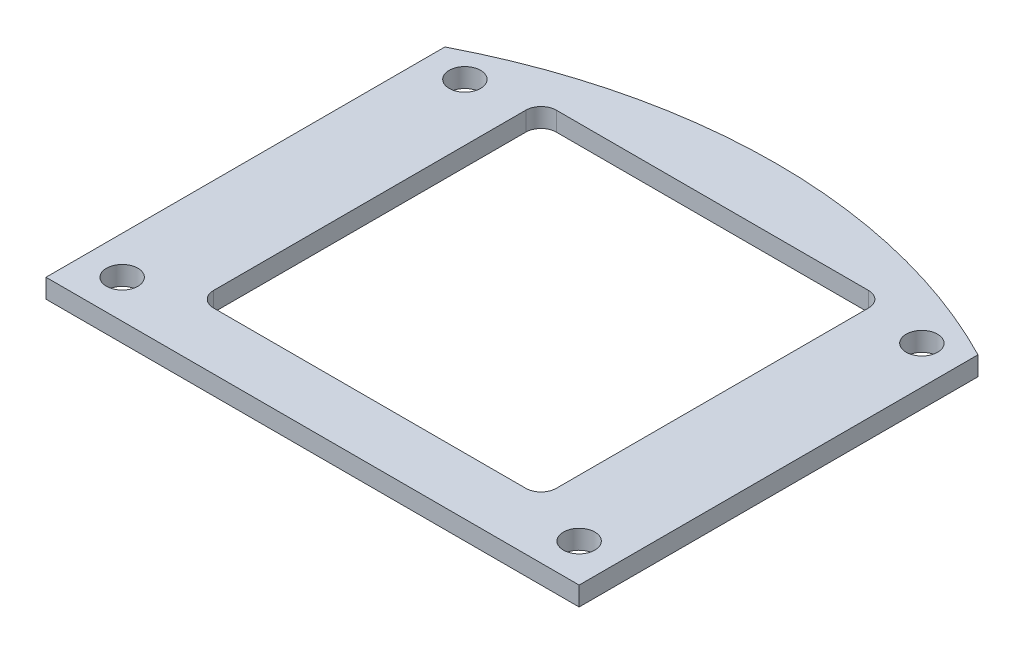
SolidWorks part; units mm, degrees
ref_plane "Front Plane" through (0, 0, 0) normal (0, 0, 1) x (1, 0, 0)
ref_plane "Top Plane" through (0, 0, 0) normal (0, 1, 0) x (1, 0, 0)
ref_plane "Right Plane" through (0, 0, 0) normal (1, 0, 0) x (0, 0, -1)
sketch "Sketch1" plane through (0, 0, 0) normal (0, 1, 0) x (1, 0, 0)
  line L1 (-28, -24) -> (28, -24)
  line L2 (-28, -24) -> (-28, 17.8957)
  line L4 (28, -24) -> (28, 17.8957)
  line L7 (-18, -18) -> (18, -18)
  line L8 (-18, -18) -> (-18, 18)
  line L9 (-18, 18) -> (18, 18)
  line L10 (18, -18) -> (18, 18)
  circle A0 centre (-24, 16) radius 1.65
  circle A1 centre (-24, -20) radius 1.65
  circle A2 centre (24, 16) radius 1.65
  circle A3 centre (24, -20) radius 1.65
  arc A4 (-17.9676, 18) -> (-18, 17.9893) centre (0, -36.3) ccw
  arc A10 (28, 17.8957) -> (-28, 17.8957) centre (0, -36.3) ccw
  arc A11 (28.3, 18.0781) -> (-28.3, 18.0781) centre (0, -36.3) ccw construction
  point P0 (0, 0)
  point P5 (0, 0)
  dimension "D5" = 16
  dimension "D6" = 4
  dimension "D7" = 4
  dimension "D8" = 16
  dimension "D9" = 3.3
  dimension "D10" = 3.3
  dimension "D11" = 4
  dimension "D12" = 4
  dimension "D13" = 4
  dimension "D15" = 3.3
  dimension "D16" = 3.3
  dimension "D17" = 4
  dimension "D22" = 0.3
  dimension "D3" = 36
  dimension "D4" = 36
  dimension "D14" = 56
  dimension "D18" = 18
  dimension "D19" = 18
  dimension "D20" = 24
  dimension "D21" = 28
extrude "Boss-Extrude1" add sketch "Sketch1" along normal blind 2
fillet "Fillet1" radius 1.6 4 edges at (-18, 1, 18) (18, 1, 18) (18, 1, -18) (-18, 1, -18)
